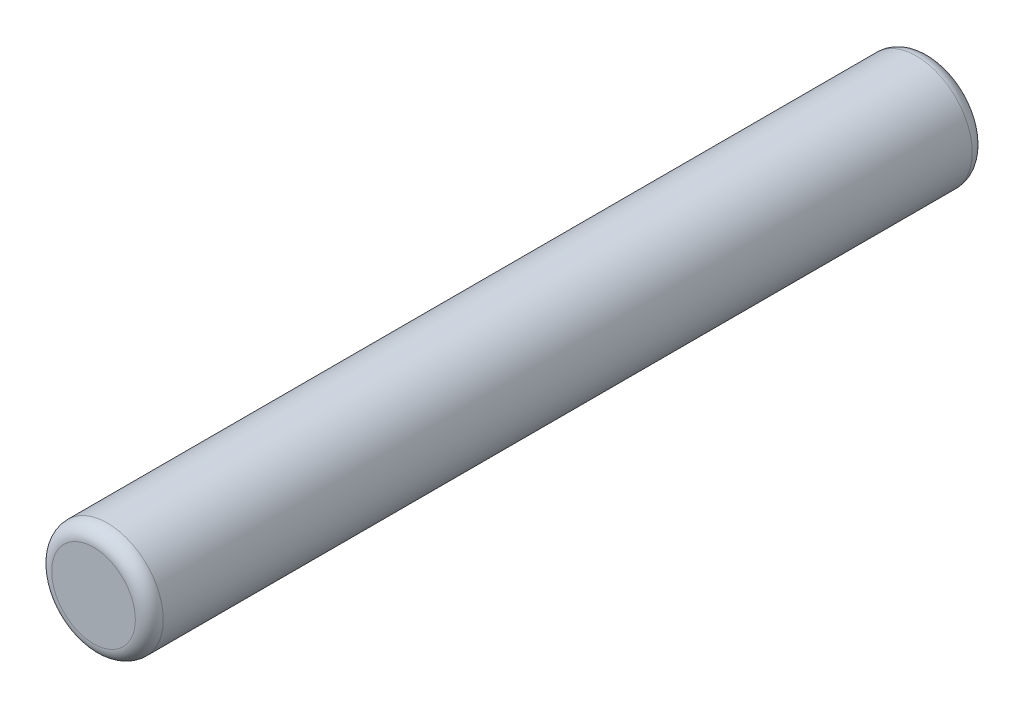
SolidWorks part; units mm, degrees
ref_plane "Front Plane" through (0, 0, 0) normal (0, 0, 1) x (1, 0, 0)
ref_plane "Top Plane" through (0, 0, 0) normal (0, 1, 0) x (1, 0, 0)
ref_plane "Right Plane" through (0, 0, 0) normal (1, 0, 0) x (0, 0, -1)
sketch "Sketch1" plane through (0, 0, 0) normal (0, 0, 1) x (1, 0, 0)
  circle A0 centre (0, 0) radius 2
  dimension "D1" = 4
extrude "Boss-Extrude1" add sketch "Sketch1" along normal mid plane 30
fillet "Fillet2" radius 0.5 2 edges at (2, 0, -15) (2, 0, 15)
